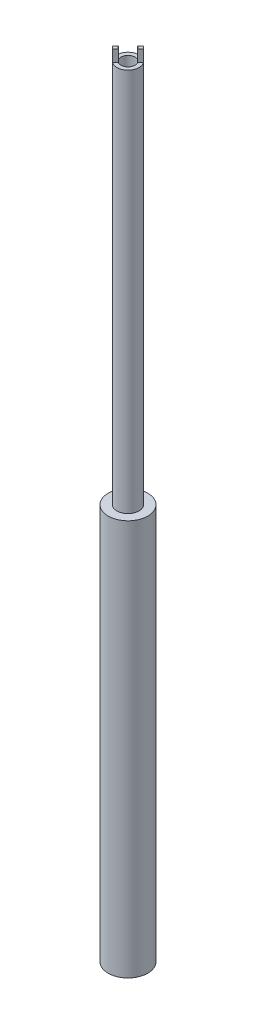
SolidWorks part; units mm, degrees
ref_plane "Front Plane" through (0, 0, 0) normal (0, 0, 1) x (1, 0, 0)
ref_plane "Top Plane" through (0, 0, 0) normal (0, 1, 0) x (1, 0, 0)
ref_plane "Right Plane" through (0, 0, 0) normal (1, 0, 0) x (0, 0, -1)
sketch "Sketch1" plane through (0, 0, 0) normal (0, 1, 0) x (1, 0, 0)
  circle A0 centre (0, 0) radius 0.889
  circle A1 centre (0, 0) radius 1.389
  dimension "D1" = 1.778
  dimension "D3" = 0.5
extrude "Boss-Extrude1" add sketch "Sketch1" along normal blind 100
sketch "Sketch2" plane through (0, 0, 0) normal (0, 1, 0) x (1, 0, 0)
  circle A0 centre (0, 0) radius 2.5
  dimension "D1" = 5
extrude "Boss-Extrude2" add sketch "Sketch2" along normal blind 50
sketch "Sketch3" plane through (0, 100, 0) normal (0, 1, 0) x (1, 0, 0)
  line L0 (-2.1213, 0) -> (0, 2.1213)
  line L1 (-1.0607, 1.0607) -> (1.0607, -1.0607) construction
  line L2 (2.1213, 0) -> (0, -2.1213)
  line L3 (0, 2.1213) -> (0.9016, 1.2198)
  line L4 (0.9016, 1.2198) -> (-1.2198, -0.9016)
  line L5 (-1.2198, -0.9016) -> (-2.1213, 0)
  line L6 (2.1213, 0) -> (1.2198, 0.9016)
  line L7 (1.2198, 0.9016) -> (-0.9016, -1.2198)
  line L8 (-0.9016, -1.2198) -> (0, -2.1213)
  line L9 (0, -2.775) -> (0, 2.8264) construction
  dimension "D1" = 3
  dimension "D2" = 0.45
  dimension "D3" = 3
  dimension "D4" = 45
extrude "Cut-Extrude1" cut sketch "Sketch3" against normal blind 1.5
